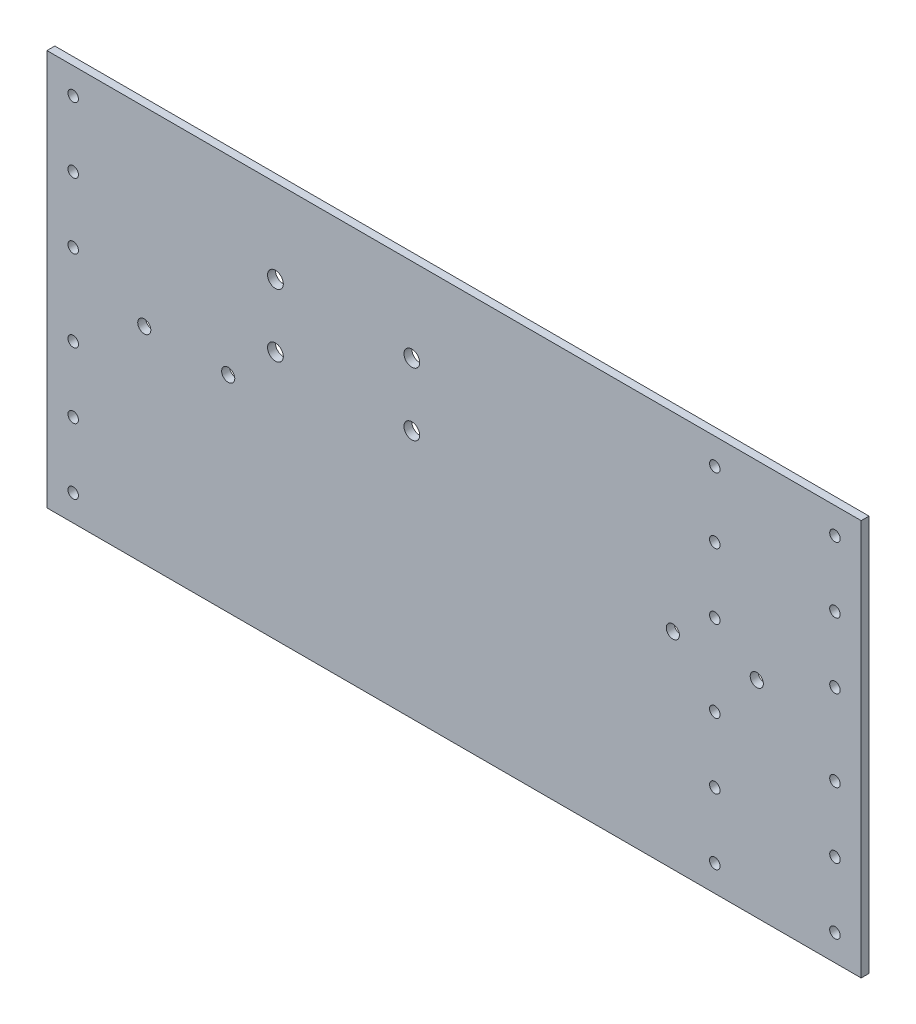
SolidWorks part; units mm, degrees
ref_plane "Ebene vorne" through (0, 0, 0) normal (0, 0, 1) x (1, 0, 0)
ref_plane "Ebene oben" through (0, 0, 0) normal (0, 1, 0) x (1, 0, 0)
ref_plane "Ebene rechts" through (0, 0, 0) normal (1, 0, 0) x (0, 0, -1)
sketch "Skizze1" plane through (0, 0, 0) normal (0, 0, 1) x (1, 0, 0)
  line L1 (0, 0) -> (310.4, 0)
  line L2 (0, 0) -> (0, 151)
  line L3 (0, 151) -> (310.4, 151)
  line L4 (310.4, 0) -> (310.4, 151)
  dimension "D1" = 310.4
  dimension "D2" = 151
extrude "Aufsatz-Linear austragen1" add sketch "Skizze1" along normal blind 3
sketch "Skizze2" plane through (0, 0, 0) normal (0, 0, -1) x (-1, 0, 0)
  line L0 (-310.4, 0) -> (-310.4, 151) construction
  line L1 (-310.4, 151) -> (0, 151) construction
  line L2 (0, 0) -> (-310.4, 0) construction
  line L3 (0, 151) -> (0, 0) construction
  circle A0 centre (-300.4, 116) radius 2
  circle A1 centre (-300.4, 141) radius 2
  circle A2 centre (-300.4, 60) radius 2
  circle A3 centre (-300.4, 91) radius 2
  circle A4 centre (-300.4, 35) radius 2
  circle A5 centre (-300.4, 10) radius 2
  circle A6 centre (-10, 141) radius 2
  circle A7 centre (-10, 116) radius 2
  circle A8 centre (-10, 91) radius 2
  circle A9 centre (-10, 60) radius 2
  circle A10 centre (-10, 35) radius 2
  circle A11 centre (-10, 10) radius 2
  dimension "D5" = 4
  dimension "D10" = 35
  dimension "D9" = 4
  dimension "D12" = 4
  dimension "D15" = 4
  dimension "D1" = 10
  dimension "D2" = 10
  dimension "D3" = 10
  dimension "D4" = 10
  dimension "D6" = 10
  dimension "D7" = 10
  dimension "D8" = 35
  dimension "D11" = 60
  dimension "D13" = 10
  dimension "D14" = 60
  dimension "D16" = 10
  dimension "D17" = 10
  dimension "D18" = 35
  dimension "D19" = 60
  dimension "D20" = 60
  dimension "D21" = 35
  dimension "D22" = 10
extrude "Schnitt-Linear austragen1" cut sketch "Skizze2" against normal blind 10
sketch "Skizze3" plane through (0, 0, 0) normal (0, 0, -1) x (-1, 0, 0)
  line L1 (0, 0) -> (-310.4, 0) construction
  line L2 (-310.4, 151) -> (0, 151) construction
  line L3 (-310.4, 0) -> (-310.4, 151) construction
  circle A0 centre (-254.6, 10) radius 2
  circle A1 centre (-254.6, 35) radius 2
  circle A2 centre (-254.6, 60) radius 2
  circle A4 centre (-254.6, 91) radius 2
  circle A5 centre (-254.6, 116) radius 2
  circle A6 centre (-254.6, 141) radius 2
  dimension "D1" = 4
  dimension "D2" = 55.8
  dimension "D3" = 10
  dimension "D4" = 10
  dimension "D5" = 35
  dimension "D6" = 35
  dimension "D7" = 60
  dimension "D8" = 60
extrude "Schnitt-Linear austragen2" cut sketch "Skizze3" against normal blind 10
sketch "Skizze4" plane through (0, 0, 0) normal (0, 0, -1) x (-1, 0, 0)
  line L1 (-310.4, 0) -> (-310.4, 151) construction
  line L2 (-310.4, 151) -> (0, 151) construction
  circle A0 centre (-139.1, 119) radius 3
  circle A1 centre (-87.1, 119) radius 3
  circle A2 centre (-139.1, 95) radius 3
  circle A3 centre (-87.1, 95) radius 3
  dimension "D1" = 6
  dimension "D2" = 32
  dimension "D3" = 171.3
  dimension "D4" = 52
  dimension "D5" = 24
extrude "Schnitt-Linear austragen3" cut sketch "Skizze4" against normal blind 10
sketch "Skizze5" plane through (0, 0, 0) normal (0, 0, -1) x (-1, 0, 0)
  line L0 (0, 0) -> (-310.4, 0) construction
  line L1 (-310.4, 0) -> (-310.4, 151) construction
  circle A0 centre (-270.6, 78.5) radius 2.5
  circle A1 centre (-238.6, 78.5) radius 2.5
  dimension "D3" = 5
  dimension "D1" = 78.5
  dimension "D2" = 39.8
  dimension "D4" = 32
extrude "Schnitt-Linear austragen4" cut sketch "Skizze5" against normal blind 10
sketch "Skizze6" plane through (0, 0, 0) normal (0, 0, -1) x (-1, 0, 0)
  line L0 (0, 151) -> (0, 0) construction
  line L1 (0, 0) -> (-310.4, 0) construction
  circle A0 centre (-69.1, 78.5) radius 2.5
  circle A1 centre (-37.1, 78.5) radius 2.5
  dimension "D1" = 5
  dimension "D2" = 37.1
  dimension "D3" = 32
  dimension "D4" = 78.5
extrude "Schnitt-Linear austragen5" cut sketch "Skizze6" against normal blind 10
